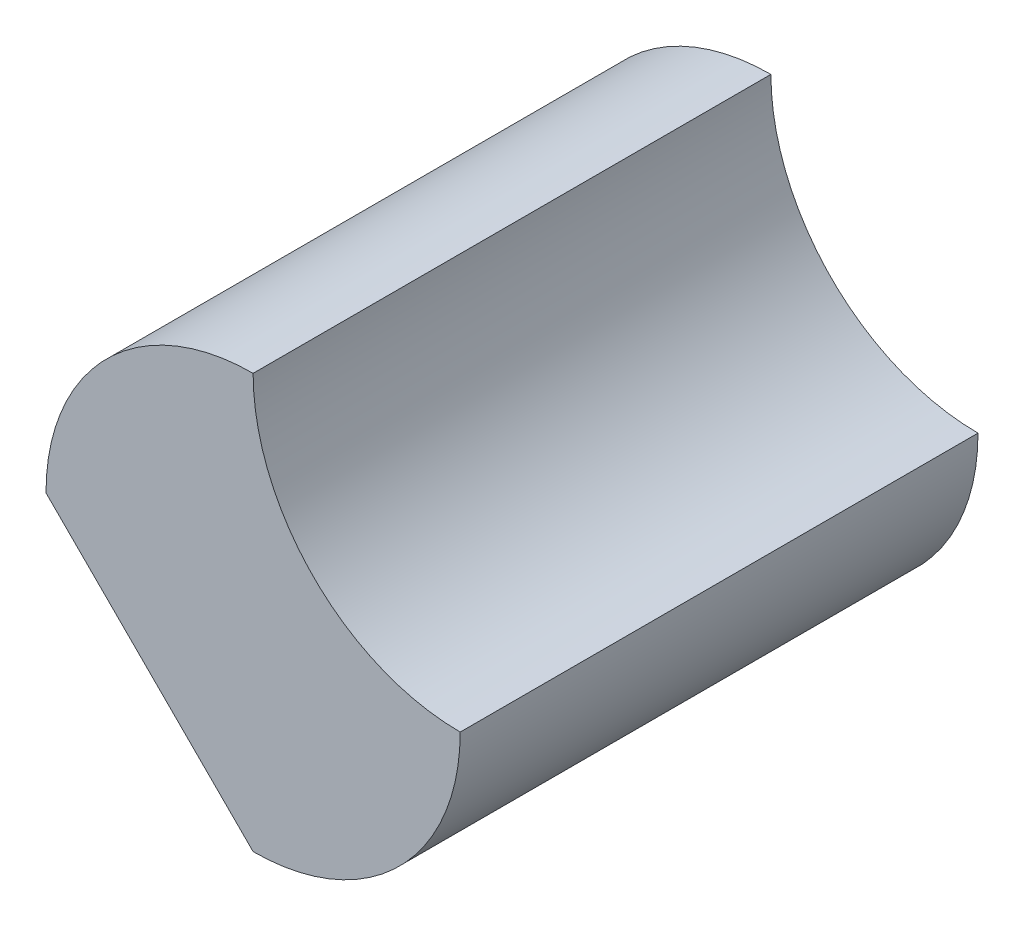
SolidWorks part; units mm, degrees
ref_plane "Front Plane" through (0, 0, 0) normal (0, 0, 1) x (1, 0, 0)
ref_plane "Top Plane" through (0, 0, 0) normal (0, 1, 0) x (1, 0, 0)
ref_plane "Right Plane" through (0, 0, 0) normal (1, 0, 0) x (0, 0, -1)
sketch "Sketch1" plane through (0, 0, 0) normal (0, 0, 1) x (1, 0, 0)
  line L0 (-10, 10) -> (0, 0)
  arc A0 (0, 0) -> (10, 10) centre (0, 10) ccw
  arc A1 (0, 20) -> (10, 10) centre (10, 20) ccw
  arc A2 (-10, 10) -> (0, 20) centre (0, 10) cw
  point P8 (0, 0)
  dimension "D3" = 10
  dimension "D4" = 10
  dimension "D5" = 10
  dimension "D1" = 10
  dimension "D2" = 10
extrude "Boss-Extrude1" add sketch "Sketch1" along normal blind 25
